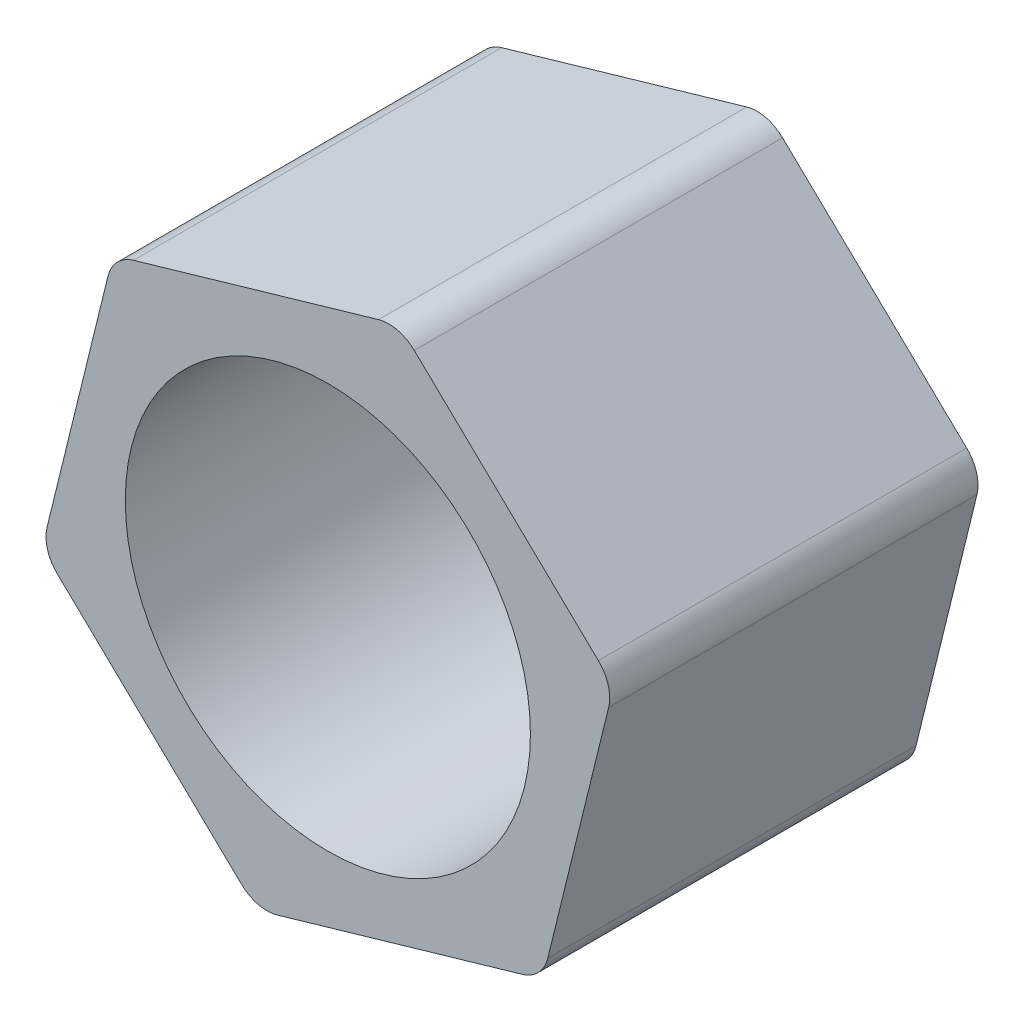
SolidWorks part; units mm, degrees
ref_plane "Front Plane" through (0, 0, 0) normal (0, 0, 1) x (1, 0, 0)
ref_plane "Top Plane" through (0, 0, 0) normal (0, 1, 0) x (1, 0, 0)
ref_plane "Right Plane" through (0, 0, 0) normal (1, 0, 0) x (0, 0, -1)
sketch "Sketch3" plane through (0, 0, 0) normal (0, 0, 1) x (1, 0, 0)
  line L1 (11.6662, -11.1907) -> (15.5246, 4.5079)
  line L2 (15.5246, 4.5079) -> (3.8583, 15.6986)
  line L3 (3.8583, 15.6986) -> (-11.6662, 11.1907)
  line L4 (-11.6662, 11.1907) -> (-15.5246, -4.5079)
  line L5 (-15.5246, -4.5079) -> (-3.8583, -15.6986)
  line L6 (-3.8583, -15.6986) -> (11.6662, -11.1907)
  circle A0 centre (0, 0) radius 11
  circle A1 centre (0, 0) radius 14 construction
  dimension "D1" = 22
  dimension "D2" = 14
extrude "Boss-Extrude1" add sketch "Sketch3" along normal blind 20
fillet "Fillet1" radius 2 6 edges at (-3.8583, -15.6986, 10) (-15.5246, -4.5079, 10) (-11.6662, 11.1907, 10) (11.6662, -11.1907, 10) (15.5246, 4.5079, 10) (3.8583, 15.6986, 10)
